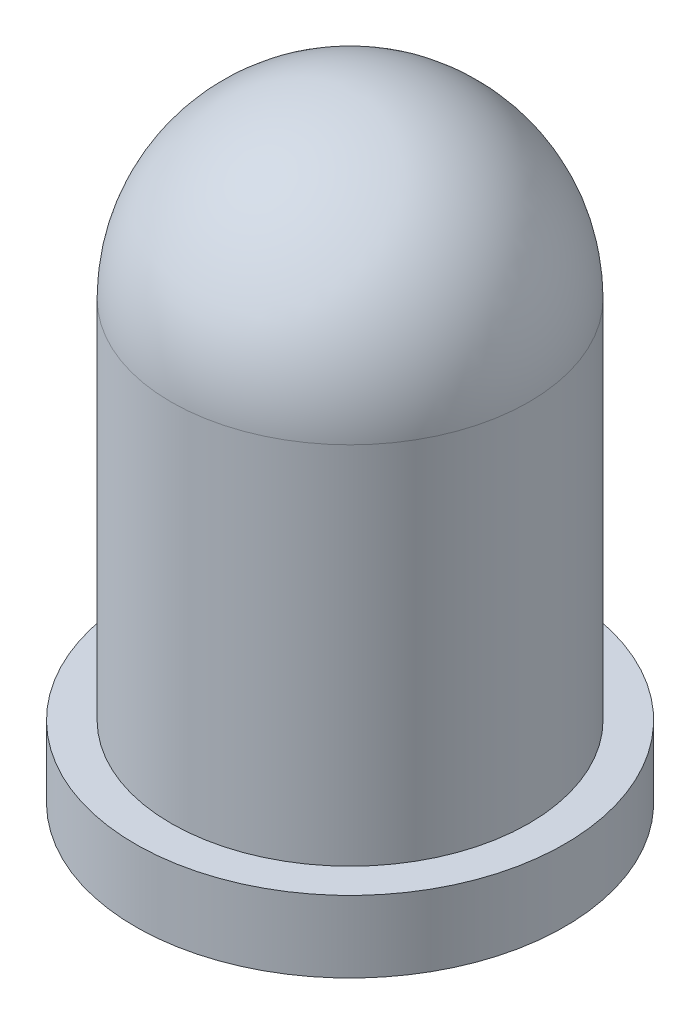
SolidWorks part; units mm, degrees
ref_plane "Front Plane" through (0, 0, 0) normal (0, 0, 1) x (1, 0, 0)
ref_plane "Top Plane" through (0, 0, 0) normal (0, 1, 0) x (1, 0, 0)
ref_plane "Right Plane" through (0, 0, 0) normal (1, 0, 0) x (0, 0, -1)
sketch "Sketch1" plane through (0, 0, 0) normal (0, 0, 1) x (1, 0, 0)
  line L0 (0, 0) -> (-3, 0)
  line L1 (-3, 0) -> (-3, 1)
  line L2 (-3, 1) -> (-2.5, 1)
  line L3 (-2.5, 1) -> (-2.5, 6.1)
  line L4 (0, 6.1) -> (0, 0)
  line L5 (-2.5, 6.1) -> (0, 6.1) construction
  line L6 (0, 6.1) -> (0, 8.6)
  arc A0 (0, 8.6) -> (-2.5, 6.1) centre (0, 6.1) ccw
  dimension "D1" = 8.6
  dimension "D2" = 2.5
  dimension "D3" = 3
  dimension "D4" = 1
revolve "Revolve3" add sketch "Sketch1" angle 360 about L4
